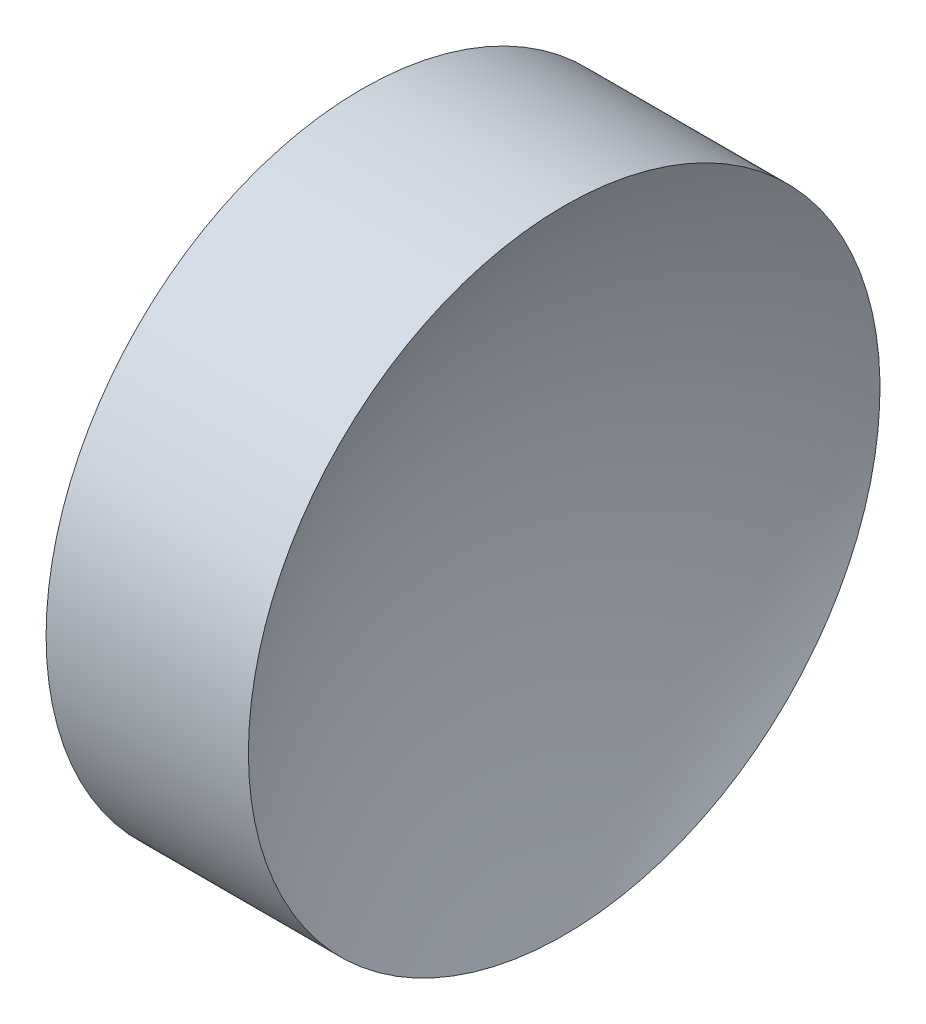
SolidWorks part; units mm, degrees
ref_plane "前视基准面" through (0, 0, 0) normal (0, 0, 1) x (1, 0, 0)
ref_plane "上视基准面" through (0, 0, 0) normal (0, 1, 0) x (1, 0, 0)
ref_plane "右视基准面" through (0, 0, 0) normal (1, 0, 0) x (0, 0, -1)
sketch "草图1" plane through (0, 0, 0) normal (0, 0, 1) x (1, 0, 0)
  line L0 (112.2415, 65.2226) -> (129.7566, 65.2226) construction
  line L1 (121.1027, 65.2226) -> (119.1027, 65.2226)
  line L3 (120.1027, 77.9226) -> (124.1707, 77.9226)
  line L4 (120.1027, 77.9226) -> (116.0347, 77.9226)
  arc A0 (119.1027, 65.2226) -> (116.0347, 77.9226) centre (91.2827, 65.2226) ccw
  arc A1 (124.1707, 77.9226) -> (121.1027, 65.2226) centre (148.9227, 65.2226) ccw
  dimension "D1" = 8.136
revolve "旋转1" add sketch "草图1" angle 360 about L0
